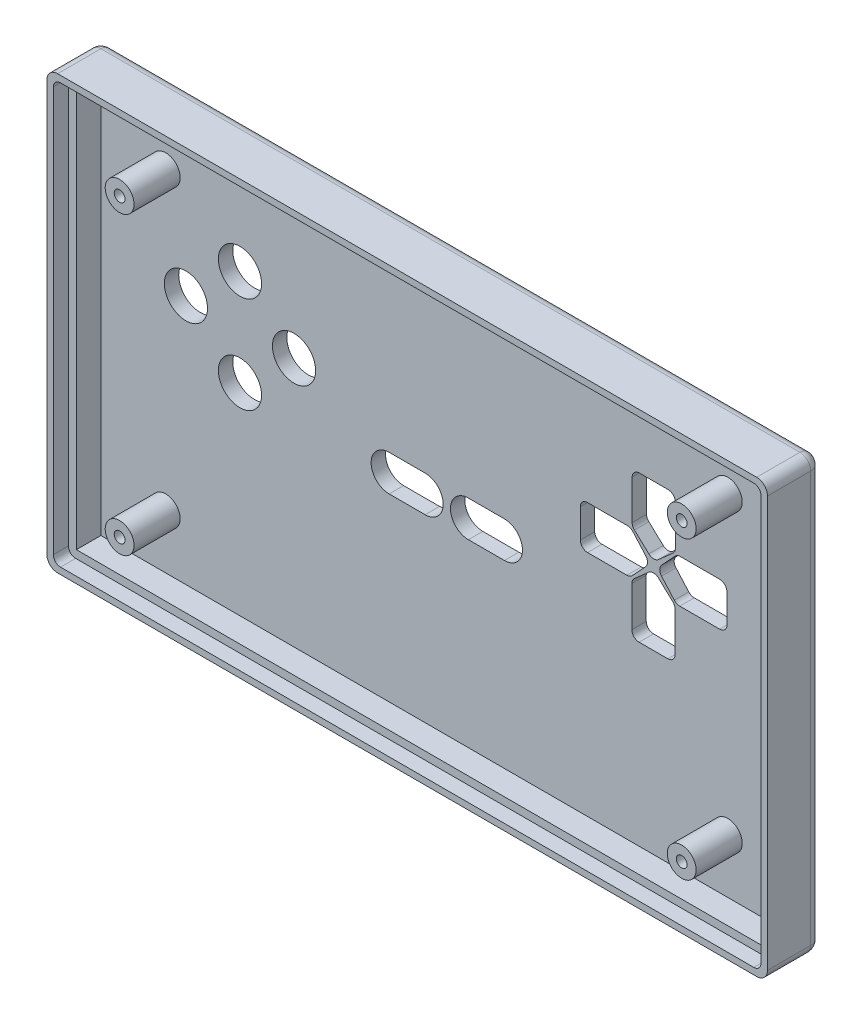
SolidWorks part; units mm, degrees
ref_plane "Front Plane" through (0, 0, 0) normal (0, 0, 1) x (1, 0, 0)
ref_plane "Top Plane" through (0, 0, 0) normal (0, 1, 0) x (1, 0, 0)
ref_plane "Right Plane" through (0, 0, 0) normal (1, 0, 0) x (0, 0, -1)
sketch "草图1" plane through (0, 0, 0) normal (0, 0, 1) x (1, 0, 0)
  line L1 (50, -30) -> (-50, -30)
  line L2 (50, -30) -> (50, 30)
  line L3 (50, 30) -> (-50, 30)
  line L4 (-50, -30) -> (-50, 30)
  line L5 (50, -30) -> (-50, 30) construction
  line L6 (50, 30) -> (-50, -30) construction
  point P0 (0, 0)
  dimension "D1" = 100
  dimension "D2" = 60
extrude "凸台-拉伸1" add sketch "草图1" along normal blind 2
sketch "草图2" plane through (0, 0, 2) normal (0, 0, 1) x (1, 0, 0)
  line L0 (50, -30) -> (50, 30) construction
  line L1 (-50, 30) -> (50, 30)
  line L2 (-50, 30) -> (-50, 28)
  line L3 (-48, 28) -> (48, 28)
  line L4 (50, 30) -> (50, 28)
  line L5 (-50, -30) -> (50, -30) construction
  line L6 (50, 30) -> (48, 30)
  line L7 (50, 30) -> (50, -30)
  line L8 (50, -30) -> (48, -30)
  line L9 (48, 28) -> (48, -28)
  line L10 (-50, 30) -> (-50, -30) construction
  line L11 (50, -30) -> (-50, -30)
  line L12 (50, -30) -> (50, -28)
  line L13 (48, -28) -> (-48, -28)
  line L14 (-50, -30) -> (-50, -28)
  line L16 (-50, -30) -> (-48, -30)
  line L17 (-50, -30) -> (-50, 30)
  line L18 (-50, 30) -> (-48, 30)
  line L19 (-48, -28) -> (-48, 28)
  line M9 (-50, 30) -> (-50, -30)
  line M10 (-50, -30) -> (50, -30)
  line M11 (50, -30) -> (50, 30)
  line M12 (50, 30) -> (-50, 30)
  dimension "D1" = 2
  dimension "D2" = 2
  dimension "D3" = 2
  dimension "D4" = 2
extrude "凸台-拉伸2" add sketch "草图2" along normal blind 5.5 contours L1 L11 L7 L13 L19 L3 L9 M12 M9 M10 M11
sketch "草图3" plane through (0, 0, 7.5) normal (0, 0, 1) x (1, 0, 0)
  line L1 (48, -28) -> (-48, -28)
  line L2 (48, -28) -> (48, 28)
  line L3 (48, 28) -> (-48, 28)
  line L4 (-48, -28) -> (-48, 28)
  line L5 (48, -28) -> (-48, 28) construction
  line L6 (48, 28) -> (-48, -28) construction
  line L7 (49.1, -29.1) -> (-49.1, -29.1)
  line L8 (49.1, -29.1) -> (49.1, 29.1)
  line L9 (49.1, 29.1) -> (-49.1, 29.1)
  line L10 (-49.1, -29.1) -> (-49.1, 29.1)
  line L11 (49.1, -29.1) -> (-49.1, 29.1) construction
  line L12 (49.1, 29.1) -> (-49.1, -29.1) construction
  point P0 (0, 0)
  point P7 (0, 0)
  dimension "D1" = 1.1
  dimension "D2" = 1.1
extrude "切除-拉伸1" cut sketch "草图3" against normal blind 2.1
fillet "圆角1" radius 1.5 8 edges at (-50, -30, 3.75) (50, -30, 3.75) (50, 30, 3.75) (-50, 30, 3.75) (50, 0, 0) (0, -30, 0) (-50, 0, 0) (0, 30, 0)
fillet "圆角2" radius 1 4 edges at (49.1, -29.1, 6.45) (49.1, 29.1, 6.45) (-49.1, -29.1, 6.45) (-49.1, 29.1, 6.45)
sketch "草图4" plane through (0, 0, 2) normal (0, 0, 1) x (1, 0, 0)
  line L1 (39, -20.5) -> (-39, -20.5) construction
  line L2 (39, -20.5) -> (39, 20.5) construction
  line L3 (39, 20.5) -> (-39, 20.5) construction
  line L4 (-39, -20.5) -> (-39, 20.5) construction
  line L5 (39, -20.5) -> (-39, 20.5) construction
  line L6 (39, 20.5) -> (-39, -20.5) construction
  circle A0 centre (-39, 20.5) radius 2
  circle A1 centre (39, 20.5) radius 2
  circle A2 centre (39, -20.5) radius 2
  circle A3 centre (-39, -20.5) radius 2
  point P0 (0, 0)
  dimension "D3" = 4
  dimension "D4" = 4
  dimension "D5" = 4
  dimension "D6" = 4
  dimension "D1" = 78
  dimension "D2" = 41
extrude "凸台-拉伸3" add sketch "草图4" along normal blind 6.4
sketch "草图5" plane through (0, 0, 8.4) normal (0, 0, 1) x (1, 0, 0)
  circle A0 centre (-39, 20.5) radius 0.75
  circle A1 centre (39, 20.5) radius 0.75
  circle A2 centre (39, -20.5) radius 0.75
  circle A3 centre (-39, -20.5) radius 0.75
extrude "切除-拉伸3" cut sketch "草图5" against normal blind 5.5
sketch "草图6" plane through (0, 0, 0) normal (0, 0, -1) x (-1, 0, 0)
  line L0 (-28.7, 34.7435) -> (-28.7, -40.4782) construction
  line L1 (-50, 28.5) -> (-50, -28.5) construction
  line L2 (-54.1379, 6.7) -> (54.6576, 6.7) construction
  line L3 (48.5, 30) -> (-48.5, 30) construction
  line L4 (-5.5, -0.5) -> (-5.5, 34.1824) construction
  line L5 (-5.5, -0.5) -> (59.6455, -0.5) construction
  line L6 (-26.0398, 9.6769) -> (-28.0354, 7.8188)
  line L8 (-31.7212, 10.3255) -> (-31.7212, 15.8753)
  line L9 (-30.7212, 16.8753) -> (-26.7212, 16.8753)
  line L10 (-25.7212, 10.4087) -> (-25.7212, 15.8753)
  line L11 (-31.7212, 9.8753) -> (-25.7212, 16.8753) construction
  line L12 (-31.7212, 16.8753) -> (-25.7212, 9.9735) construction
  line L13 (-29.3798, 7.802) -> (-31.3841, 9.5768)
  line L14 (0, 0) -> (0, -5.7355) construction
  line L15 (-25.7231, 4.0398) -> (-27.5812, 6.0354)
  line L16 (-25.0745, 9.7212) -> (-19.5247, 9.7212)
  line L17 (-18.5247, 8.7212) -> (-18.5247, 4.7212)
  line L18 (-24.9913, 3.7212) -> (-19.5247, 3.7212)
  line L19 (-27.598, 7.3798) -> (-25.8232, 9.3841)
  line L20 (-31.3602, 3.7231) -> (-29.3646, 5.5812)
  line L21 (-25.6788, 3.0745) -> (-25.6788, -2.4753)
  line L22 (-26.6788, -3.4753) -> (-30.6788, -3.4753)
  line L23 (-31.6788, 2.9913) -> (-31.6788, -2.4753)
  line L24 (-28.0202, 5.598) -> (-26.0159, 3.8232)
  line L25 (-31.6769, 9.3602) -> (-29.8188, 7.3646)
  line L26 (-32.3255, 3.6788) -> (-37.8753, 3.6788)
  line L27 (-38.8753, 4.6788) -> (-38.8753, 8.6788)
  line L28 (-32.4087, 9.6788) -> (-37.8753, 9.6788)
  line L29 (-29.802, 6.0202) -> (-31.5768, 4.0159)
  line L30 (-8, -3) -> (-3, -3)
  line L32 (-8, 2) -> (-3, 2)
  line L34 (-8, -3) -> (-3, 2) construction
  line L35 (-8, 2) -> (-3, -3) construction
  line L36 (8, 2) -> (3, 2)
  line L37 (8, -3) -> (3, -3)
  arc A0 (-29.3798, 7.802) -> (-28.0354, 7.8188) centre (-28.7169, 8.5506) ccw
  arc A1 (-25.7212, 10.4087) -> (-26.0398, 9.6769) centre (-26.7212, 10.4087) cw
  arc A2 (-31.3841, 9.5768) -> (-31.7212, 10.3255) centre (-30.7212, 10.3255) cw
  arc A3 (-31.7212, 15.8753) -> (-30.7212, 16.8753) centre (-30.7212, 15.8753) cw
  arc A4 (-26.7212, 16.8753) -> (-25.7212, 15.8753) centre (-26.7212, 15.8753) cw
  arc A5 (-27.598, 7.3798) -> (-27.5812, 6.0354) centre (-26.8494, 6.7169) ccw
  arc A6 (-24.9913, 3.7212) -> (-25.7231, 4.0398) centre (-24.9913, 4.7212) cw
  arc A7 (-25.8232, 9.3841) -> (-25.0745, 9.7212) centre (-25.0745, 8.7212) cw
  arc A8 (-19.5247, 9.7212) -> (-18.5247, 8.7212) centre (-19.5247, 8.7212) cw
  arc A9 (-18.5247, 4.7212) -> (-19.5247, 3.7212) centre (-19.5247, 4.7212) cw
  arc A10 (-28.0202, 5.598) -> (-29.3646, 5.5812) centre (-28.6831, 4.8494) ccw
  arc A11 (-31.6788, 2.9913) -> (-31.3602, 3.7231) centre (-30.6788, 2.9913) cw
  arc A12 (-26.0159, 3.8232) -> (-25.6788, 3.0745) centre (-26.6788, 3.0745) cw
  arc A13 (-25.6788, -2.4753) -> (-26.6788, -3.4753) centre (-26.6788, -2.4753) cw
  arc A14 (-30.6788, -3.4753) -> (-31.6788, -2.4753) centre (-30.6788, -2.4753) cw
  arc A15 (-29.802, 6.0202) -> (-29.8188, 7.3646) centre (-30.5506, 6.6831) ccw
  arc A16 (-32.4087, 9.6788) -> (-31.6769, 9.3602) centre (-32.4087, 8.6788) cw
  arc A17 (-31.5768, 4.0159) -> (-32.3255, 3.6788) centre (-32.3255, 4.6788) cw
  arc A18 (-37.8753, 3.6788) -> (-38.8753, 4.6788) centre (-37.8753, 4.6788) cw
  arc A19 (-38.8753, 8.6788) -> (-37.8753, 9.6788) centre (-37.8753, 8.6788) cw
  arc A20 (-3, -3) -> (-3, 2) centre (-3, -0.5) ccw
  arc A21 (-8, 2) -> (-8, -3) centre (-8, -0.5) ccw
  arc A22 (8, 2) -> (8, -3) centre (8, -0.5) cw
  arc A23 (3, -3) -> (3, 2) centre (3, -0.5) cw
  circle A24 centre (28.7, 13.4) radius 3
  circle A25 centre (36.2, 6.7) radius 3
  circle A26 centre (28.7, 0) radius 3
  circle A27 centre (21.2, 6.7) radius 3
  point P15 (-28.7, 13.4)
  point P22 (-28.7, 7.2)
  point P40 (-22, 6.7)
  point P56 (-28.7, 0)
  point P72 (-35.4, 6.7)
  point P86 (-28.7, 6.7)
  dimension "D8" = 1
  dimension "D1" = 21.3
  dimension "D2" = 23.3
  dimension "D3" = 44.5
  dimension "D4" = 30.5
  dimension "D5" = 6
  dimension "D6" = 7
  dimension "D7" = 0.5
  dimension "D10" = 5
  dimension "D11" = 5
  dimension "D9" = 4
extrude "切除-拉伸4" cut sketch "草图6" against normal blind 10 contours A23 L37 A22 L36 | A27 | A24 | A25 | A26 | L6 A0 L13 A2 L8 A3 L9 A4 L10 A1 | L15 A5 L19 A7 L16 A8 L17 A9 L18 A6 | L20 A10 L24 A12 L21 A13 L22 A14 L23 A11 | L29 A17 L26 A18 L27 A19 L28 A16 L25 A15 | L32 A20 L30 A21
